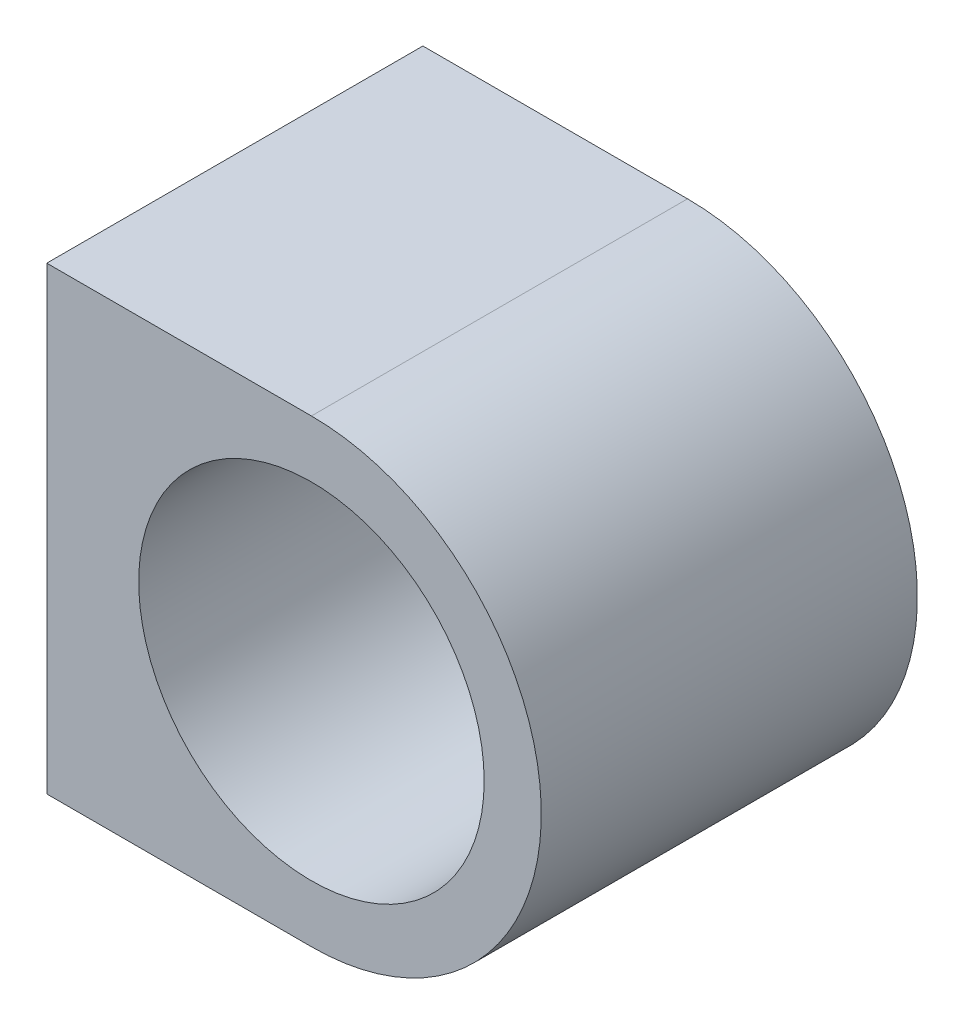
SolidWorks part; units mm, degrees
ref_plane "Front Plane" through (0, 0, 0) normal (0, 0, 1) x (1, 0, 0)
ref_plane "Top Plane" through (0, 0, 0) normal (0, 1, 0) x (1, 0, 0)
ref_plane "Right Plane" through (0, 0, 0) normal (1, 0, 0) x (0, 0, -1)
sketch "Sketch1" plane through (0, 0, 0) normal (0, 0, 1) x (1, 0, 0)
  line L0 (-9.5, 8.25) -> (-9.5, -8.25)
  line L1 (0, 8.25) -> (-9.5, 8.25)
  line L2 (0, -8.25) -> (-9.5, -8.25)
  circle A3 centre (0, 0) radius 6.2
  arc A4 (0, -8.25) -> (0, 8.25) centre (0, 0) ccw
  dimension "D1" = 12.4
  dimension "D2" = 16.5
  dimension "D3" = 9.5
extrude "Boss-Extrude1" add sketch "Sketch1" along normal blind 13.5
hole_wizard "Ø2.7 (2.7) Diameter Hole1" positions "Sketch5" profile "Sketch4" hole size "Ø2.7" standard "Ansi Metric"
sketch "Sketch5" plane through (-9.5, 0, 0) normal (-1, 0, 0) x (0, 0, 1)
  line L1 (2.5, -5) -> (11, -5) construction
  line L2 (2.5, -5) -> (2.5, 5) construction
  line L3 (2.5, 5) -> (11, 5) construction
  line L4 (11, -5) -> (11, 5) construction
  line L5 (0, 0) -> (2.5, 0) construction
  line L7 (0, 8.25) -> (0, -8.25) construction
  line L10 (13.5, 0) -> (11, 0) construction
  line L11 (13.5, 8.25) -> (13.5, -8.25) construction
  point P0 (2.5, -5)
  point P89 (2.5, 5)
  point P91 (11, 5)
  point P93 (11, -5)
  dimension "D1" = 2.5
  dimension "D2" = 10
sketch "Sketch4" plane through (-9.5, -5, 2.5) normal (0, 1, 0) x (0, 0, 1)
  line L0 (0, 0) -> (0, 4.8112)
  line L1 (0, 4.8112) -> (1.35, 4)
  line L2 (1.35, 4) -> (1.35, 0)
  line L5 (1.35, 0) -> (0, 0)
  line L10 (0, 4.8112) -> (-1.35, 4) construction
  line L11 (0, -6.35) -> (0, 107.95) construction
  dimension "Hole Dia." = 2.7
  dimension "Hole Depth" = 4
  dimension "Drill Angle" = 118
